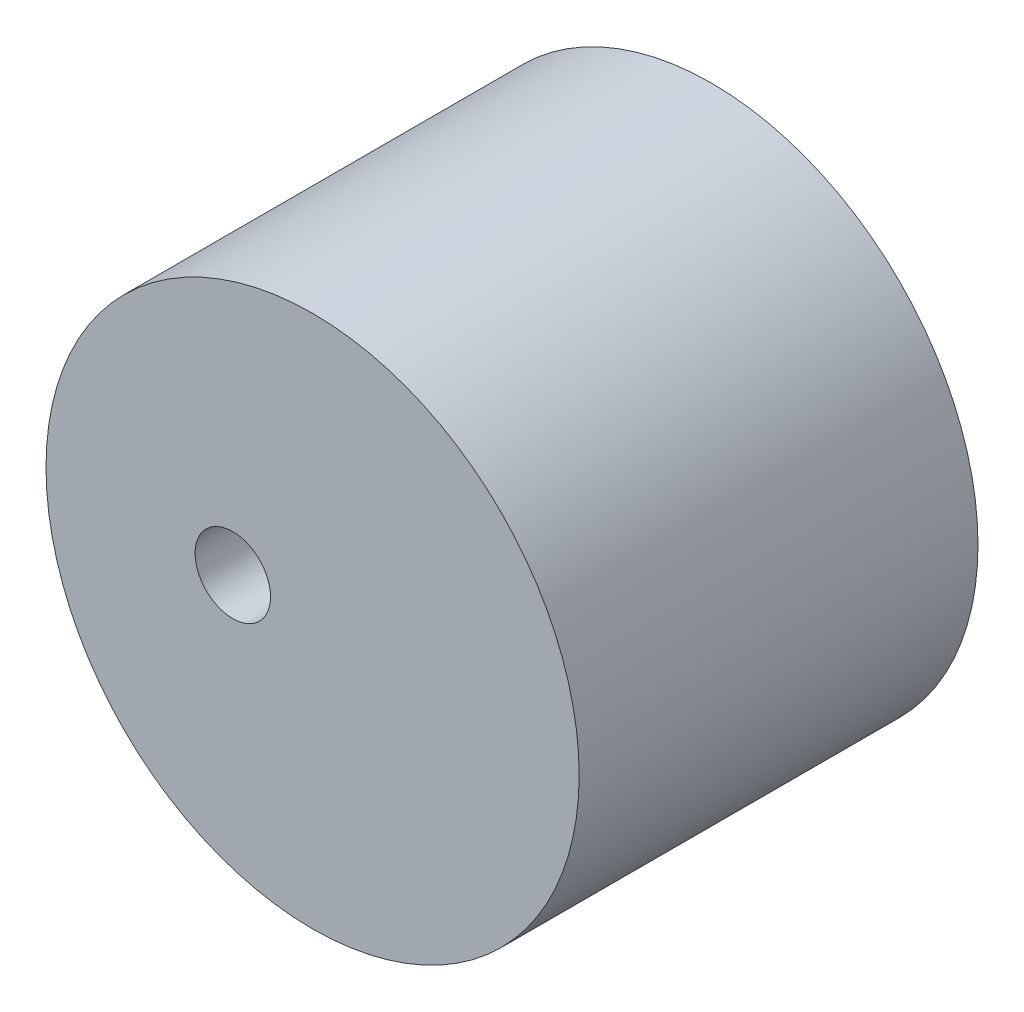
SolidWorks part; units mm, degrees
ref_plane "Front Plane" through (0, 0, 0) normal (0, 0, 1) x (1, 0, 0)
ref_plane "Top Plane" through (0, 0, 0) normal (0, 1, 0) x (1, 0, 0)
ref_plane "Right Plane" through (0, 0, 0) normal (1, 0, 0) x (0, 0, -1)
sketch "Sketch11" plane through (0, 0, 0) normal (0, 0, 1) x (1, 0, 0)
  circle A0 centre (0, 0) radius 23.3938
  circle A1 centre (-7, 0) radius 3.3085
  point P4 (0, 0)
extrude "Boss-Extrude13" add sketch "Sketch11" along normal blind 35
